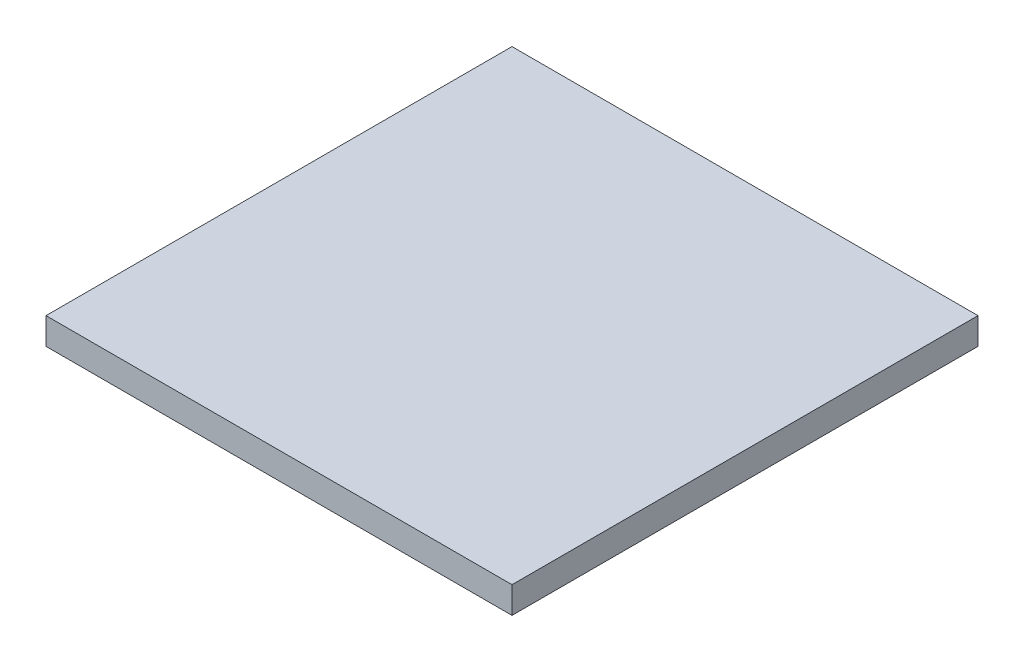
SolidWorks part; units mm, degrees
ref_plane "Front Plane" through (0, 0, 0) normal (0, 0, 1) x (1, 0, 0)
ref_plane "Top Plane" through (0, 0, 0) normal (0, 1, 0) x (1, 0, 0)
ref_plane "Right Plane" through (0, 0, 0) normal (1, 0, 0) x (0, 0, -1)
sketch "Sketch1" plane through (0, 0, 0) normal (0, 1, 0) x (1, 0, 0)
  line L1 (17.5, 17.5) -> (-17.5, 17.5)
  line L2 (17.5, 17.5) -> (17.5, -17.5)
  line L3 (17.5, -17.5) -> (-17.5, -17.5)
  line L4 (-17.5, 17.5) -> (-17.5, -17.5)
  line L5 (17.5, 17.5) -> (-17.5, -17.5) construction
  line L6 (17.5, -17.5) -> (-17.5, 17.5) construction
  point P0 (0, 0)
  dimension "D1" = 35
  dimension "D2" = 35
extrude "Boss-Extrude1" add sketch "Sketch1" along normal blind 2
